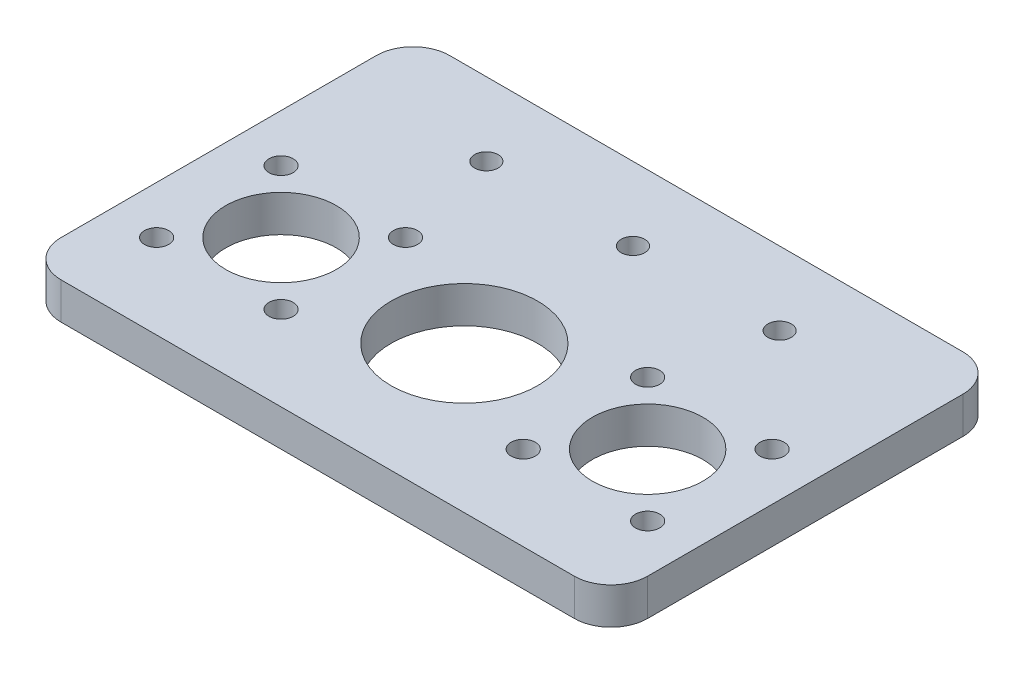
SolidWorks part; units mm, degrees
ref_plane "前视基准面" through (0, 0, 0) normal (0, 0, 1) x (1, 0, 0)
ref_plane "上视基准面" through (0, 0, 0) normal (0, 1, 0) x (1, 0, 0)
ref_plane "右视基准面" through (0, 0, 0) normal (1, 0, 0) x (0, 0, -1)
sketch "草图1" plane through (0, 0, 0) normal (0, 1, 0) x (1, 0, 0)
  line L0 (-107.5099, 0) -> (110.7056, 0) construction
  line L1 (0, 60.3977) -> (0, -44.8569) construction
  line L2 (-25, 60.3977) -> (-25, -44.8569) construction
  line L3 (25, 60.3977) -> (25, -44.8569) construction
  line L4 (-25, 0) -> (-39.1277, 14.1277) construction
  line L5 (-25, 82.5099) -> (-25, -135.7056) construction
  line L6 (57.5099, 0) -> (-160.7056, 0) construction
  line L7 (-25, -82.5099) -> (-25, 135.7056) construction
  line L8 (-107.5099, 23) -> (110.7056, 23) construction
  line L9 (-20, 60.3977) -> (-20, -44.8569) construction
  line L10 (20, 60.3977) -> (20, -44.8569) construction
  line L11 (-35, 33) -> (35, 33)
  line L12 (-40, 28) -> (-40, -15)
  line L13 (40, 28) -> (40, -15)
  line L14 (-35, -20) -> (35, -20)
  line L15 (-40, 60.3977) -> (-40, -44.8569) construction
  line L16 (-107.5099, -20) -> (110.7056, -20) construction
  line L17 (40, 60.3977) -> (40, -44.8569) construction
  line L18 (-107.5099, 33) -> (110.7056, 33) construction
  circle A0 centre (0, 0) radius 10
  circle A1 centre (0, 0) radius 10 construction
  circle A6 centre (-25, 0) radius 7.55
  circle A7 centre (-25, 0) radius 12 construction
  circle A8 centre (-33.4853, 8.4853) radius 1.65
  circle A9 centre (-16.5147, 8.4853) radius 1.65
  circle A10 centre (-16.5147, -8.4853) radius 1.65
  circle A11 centre (-33.4853, -8.4853) radius 1.65
  circle A12 centre (-16.5147, 8.4853) radius 1.65
  circle A13 centre (-33.4853, -8.4853) radius 1.65
  circle A14 centre (25, 0) radius 7.55
  circle A15 centre (16.5147, 8.4853) radius 1.65
  circle A16 centre (16.5147, -8.4853) radius 1.65
  circle A17 centre (33.4853, -8.4853) radius 1.65
  circle A18 centre (33.4853, 8.4853) radius 1.65
  circle A19 centre (-20, 23) radius 1.6
  circle A20 centre (0, 23) radius 1.6
  circle A21 centre (20, 23) radius 1.6
  arc A22 (-40, -15) -> (-35, -20) centre (-35, -15) ccw
  arc A23 (35, -20) -> (40, -15) centre (35, -15) ccw
  arc A24 (40, 28) -> (35, 33) centre (35, 28) ccw
  arc A25 (-35, 33) -> (-40, 28) centre (-35, 28) ccw
  dimension "D2" = 20
  dimension "D3" = 20
  dimension "D7" = 24
  dimension "D8" = 15.1
  dimension "D10" = 3.3
  dimension "D15" = 3.2
  dimension "D21" = 5
  dimension "D9" = 45
  dimension "D5" = 25
  dimension "D6" = 25
  dimension "D12" = 23
  dimension "D13" = 20
  dimension "D14" = 20
  dimension "D17" = 10
  dimension "D18" = 40
  dimension "D19" = 40
  dimension "D20" = 53
  dimension "D16" = 3
  dimension "D11" = 4
extrude "凸台-拉伸1" add sketch "草图1" along normal blind 5
